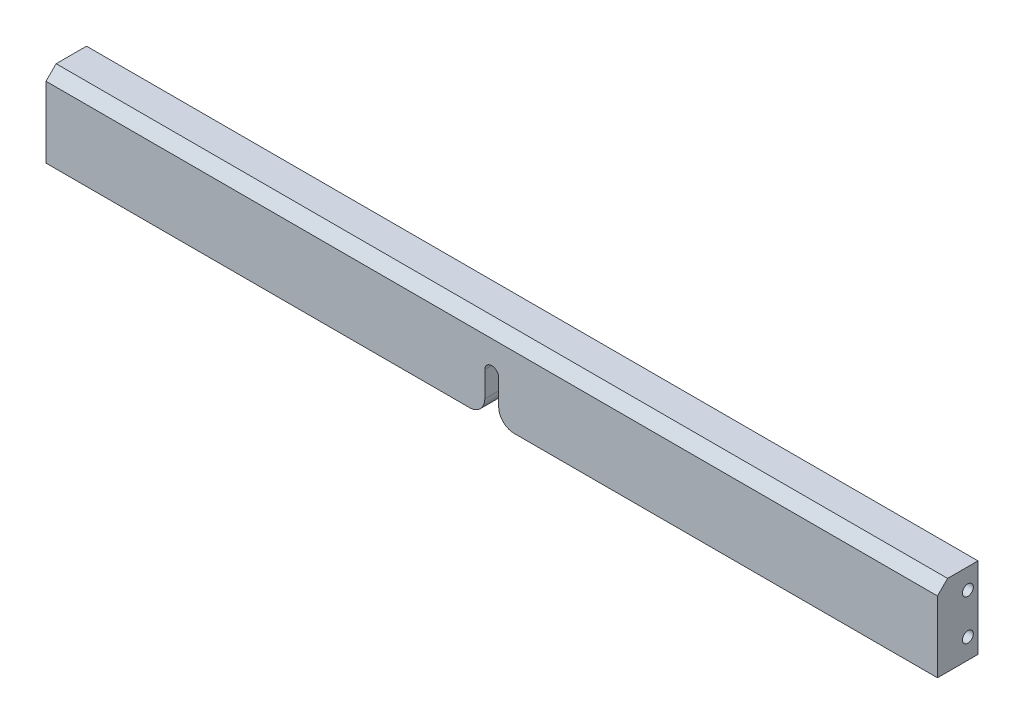
SolidWorks part; units mm, degrees
material "Alum 6061 (Default)"
ref_plane "Front Plane" through (0, 0, 0) normal (0, 0, 1) x (1, 0, 0)
ref_plane "Top Plane" through (0, 0, 0) normal (0, 1, 0) x (1, 0, 0)
ref_plane "Right Plane" through (0, 0, 0) normal (1, 0, 0) x (0, 0, -1)
sketch "Sketch1" plane through (0, 0, 0) normal (0, 0, 1) x (1, 0, 0)
  line L1 (-279.4, 25.4) -> (279.4, 25.4)
  line L2 (-279.4, 25.4) -> (-279.4, -25.4)
  line L3 (-279.4, -25.4) -> (279.4, -25.4)
  line L4 (279.4, 25.4) -> (279.4, -25.4)
  line L5 (-279.4, 25.4) -> (279.4, -25.4) construction
  line L6 (-279.4, -25.4) -> (279.4, 25.4) construction
  point P0 (0, 0)
  dimension "SpreadWidthB" = 558.8
  dimension "Height" = 50.8
extrude "Extrude1" add sketch "Sketch1" along normal mid plane 25.4
sketch "Sketch4" plane through (0, 0, 12.7) normal (0, 0, 1) x (1, 0, 0)
  line L0 (0, -25.4) -> (0, 0) construction
  line L1 (-279.4, -25.4) -> (279.4, -25.4) construction
  line L2 (-4.3656, -25.4) -> (-4.3656, 0)
  line L3 (4.3656, -25.4) -> (4.3656, 0)
  arc A0 (-4.3656, -25.4) -> (4.3656, -25.4) centre (0, -25.4) ccw
  arc A1 (4.3656, 0) -> (-4.3656, 0) centre (0, 0) ccw
  point P5 (0, -12.7)
  dimension "D1" = 8.7312
  dimension "D2" = 25.4
extrude "Cut-Extrude3" cut sketch "Sketch4" against normal up to next
fillet "Fillet2" radius 9.525 2 edges at (4.3656, -25.4, 0) (-4.3656, -25.4, 0)
hole_wizard "M8x1.25 Tapped Hole1" positions "Sketch6" profile "Sketch7" tap size "M8x1.25" standard "ANSI Metric"
sketch "Sketch6" plane through (279.4, 0, 0) normal (1, 0, 0) x (0, 0, -1)
  line L0 (6.35, 12.7) -> (6.35, -12.7) construction
  line L1 (12.7, -25.4) -> (12.7, 25.4) construction
  point P0 (6.35, 12.7)
  point P2 (6.35, -12.7)
  point P18 (6.35, 0)
  dimension "D1" = 25.4
  dimension "D2" = 6.35
sketch "Sketch7" plane through (279.4, 12.7, -6.35) normal (0, 1, 0) x (0, 0, -1)
  line L0 (0, 0) -> (0, 21.8549)
  line L1 (0, 21.8549) -> (3.4, 19.812)
  line L2 (3.4, 19.812) -> (3.4, 0)
  line L5 (3.4, 0) -> (0, 0)
  line L10 (0, 21.8549) -> (-3.4, 19.812) construction
  line L11 (0, -6.35) -> (0, 107.95) construction
  dimension "Tap Drill Dia." = 6.8
  dimension "Tap Drill Depth" = 19.812
  dimension "Drill Angle" = 118
cosmetic thread "Hole Thread1" parameters "D1"=16.002, "D2"=8
cosmetic thread "Hole Thread2" parameters "D1"=16.002, "D2"=8
hole_wizard "M8x1.25 Tapped Hole2" positions "Sketch8" profile "Sketch9" tap size "M8x1.25" standard "ANSI Metric"
sketch "Sketch8" plane through (-279.4, 0, 0) normal (-1, 0, 0) x (0, 0, 1)
  point P0 (-6.35, 12.7)
  point P2 (-6.35, -12.7)
sketch "Sketch9" plane through (-279.4, 12.7, -6.35) normal (0, 1, 0) x (0, 0, 1)
  line L0 (0, 0) -> (0, 21.8549)
  line L1 (0, 21.8549) -> (3.4, 19.812)
  line L2 (3.4, 19.812) -> (3.4, 0)
  line L5 (3.4, 0) -> (0, 0)
  line L10 (0, 21.8549) -> (-3.4, 19.812) construction
  line L11 (0, -6.35) -> (0, 107.95) construction
  dimension "Tap Drill Dia." = 6.8
  dimension "Tap Drill Depth" = 19.812
  dimension "Drill Angle" = 118
cosmetic thread "Hole Thread3" parameters "D1"=16.002, "D2"=8
cosmetic thread "Hole Thread4" parameters "D1"=16.002, "D2"=8
chamfer "Chamfer1" distance 6.35 angle 45 1 edges at (0, 25.4, 12.7)
